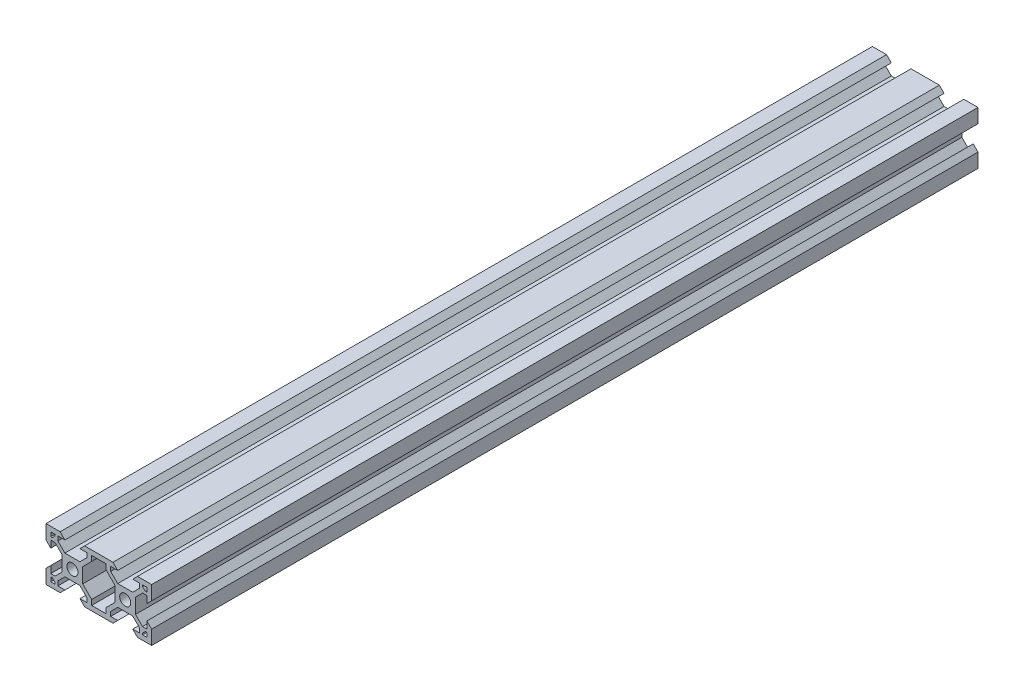
SolidWorks part; units mm, degrees
ref_plane "Front Plane" through (0, 0, 0) normal (0, 0, 1) x (1, 0, 0)
ref_plane "Top Plane" through (0, 0, 0) normal (0, 1, 0) x (1, 0, 0)
ref_plane "Right Plane" through (0, 0, 0) normal (1, 0, 0) x (0, 0, -1)
sketch "Sketch1" plane through (0, 0, 0) normal (0, 0, 1) x (1, 0, 0)
  line L0 (0, 0) -> (0, 5.36)
  line L1 (0, 20) -> (5.36, 20)
  line L3 (20, 0) -> (14.64, 0)
  line L4 (0, 10) -> (20, 10) construction
  line L5 (5.36, 0) -> (0, 0)
  line L6 (4.5007, 18.2) -> (7.16, 18.2)
  line L7 (17.3007, 3.76) -> (17.3007, 1.8)
  line L8 (15.4993, 1.8) -> (12.84, 1.8)
  line L9 (20, 0) -> (0, 0) construction
  line L10 (7.16, 1.8) -> (4.5007, 1.8)
  line L11 (15.4993, 3.44) -> (12.84, 6.0993)
  line L12 (4.5007, 16.56) -> (7.16, 13.9007)
  line L13 (13.9007, 12.84) -> (13.9007, 7.16)
  line L14 (12.84, 13.9007) -> (7.16, 13.9007)
  line L15 (6.0993, 12.84) -> (6.0993, 7.16)
  line L16 (7.16, 6.0993) -> (12.84, 6.0993)
  line L17 (4.5007, 16.56) -> (4.5007, 18.2)
  line L18 (3.44, 15.4993) -> (1.8, 15.4993)
  line L19 (4.5007, 3.44) -> (4.5007, 1.8)
  line L20 (3.44, 4.5007) -> (1.8, 4.5007)
  line L21 (15.4993, 3.44) -> (15.4993, 1.8)
  line L23 (17.3007, 1.8) -> (22.7007, 1.8)
  line L24 (15.4993, 16.56) -> (15.4993, 18.2)
  line L25 (7.16, 18.2) -> (5.36, 20)
  line L26 (12.84, 1.8) -> (14.64, 0)
  line L27 (7.16, 1.8) -> (5.36, 0)
  line L28 (12.84, 18.2) -> (14.64, 20)
  line L29 (1.8, 7.16) -> (0, 5.36)
  line L30 (1.8, 12.84) -> (0, 14.64)
  line L31 (22.7007, 1.8) -> (22.7007, 3.76)
  line L32 (17.3007, 16.24) -> (17.3007, 18.2)
  line L33 (17.3007, 18.2) -> (22.6993, 18.2)
  line L34 (22.6993, 18.2) -> (22.6993, 16.24)
  line L35 (38.2013, 12.8423) -> (40.001, 14.6427)
  line L36 (38.2024, 7.1623) -> (40.0028, 5.3627)
  line L37 (27.16, 18.2) -> (25.36, 20)
  line L38 (32.84, 1.8) -> (34.64, 0)
  line L39 (27.16, 1.8) -> (25.36, 0)
  line L40 (32.84, 18.2) -> (34.64, 20)
  line L41 (24.5013, 16.5597) -> (24.5009, 18.2)
  line L42 (1.8, 18.2) -> (3.4307, 18.2)
  line L43 (3.4307, 18.2) -> (3.4307, 17.63)
  line L44 (24.5038, 3.4397) -> (24.5041, 1.8)
  line L45 (36.5629, 4.5027) -> (38.2029, 4.503)
  line L46 (35.5025, 3.4418) -> (35.5028, 1.8)
  line L47 (36.5608, 15.5014) -> (38.2008, 15.5017)
  line L48 (35.4999, 16.5618) -> (35.4996, 18.2)
  line L49 (32.8426, 6.1006) -> (27.1626, 6.0995)
  line L50 (33.902, 12.8415) -> (33.9031, 7.1615)
  line L51 (27.1611, 13.9009) -> (32.8411, 13.902)
  line L52 (26.1007, 12.84) -> (26.1007, 7.16)
  line L53 (1.8, 4.5007) -> (1.8, 7.16)
  line L54 (24.5038, 3.4397) -> (27.1626, 6.0995)
  line L55 (35.5025, 3.4418) -> (32.8426, 6.1006)
  line L56 (36.5629, 4.5027) -> (33.9031, 7.1615)
  line L57 (24.5041, 1.8) -> (27.16, 1.8)
  line L58 (3.4307, 17.63) -> (2.37, 16.5693)
  line L59 (3.44, 4.5007) -> (6.0993, 7.16)
  line L60 (35.4996, 18.2) -> (32.84, 18.2)
  line L61 (20, 0) -> (25.36, 0)
  line L62 (39.9999, 20) -> (34.64, 20)
  line L63 (40.0038, 0) -> (40.0028, 5.3627)
  line L64 (1.8, 12.84) -> (1.8, 15.4993)
  line L65 (1.8, 1.8) -> (1.8, 18.2) construction
  line L66 (0, 14.64) -> (0, 20)
  line L67 (0, 0) -> (0, 20) construction
  line L68 (14.64, 20) -> (20, 20)
  line L69 (0, 20) -> (20, 20) construction
  line L70 (12.84, 18.2) -> (15.4993, 18.2)
  line L71 (1.8, 18.2) -> (18.2, 18.2) construction
  line L72 (25.36, 20) -> (20, 20)
  line L73 (27.16, 18.2) -> (24.5009, 18.2)
  line L74 (38.2013, 12.8423) -> (38.2008, 15.5017)
  line L75 (40.001, 14.6427) -> (39.9999, 20)
  line L76 (32.84, 1.8) -> (35.5028, 1.8)
  line L77 (34.64, 0) -> (40.0038, 0)
  line L78 (38.2029, 4.503) -> (38.2024, 7.1623)
  line L79 (35.4999, 16.5618) -> (32.8411, 13.902)
  line L80 (4.5007, 3.44) -> (7.16, 6.0993)
  line L81 (2.37, 16.5693) -> (1.8, 16.5693)
  line L82 (18.2, 1.8) -> (1.8, 1.8) construction
  line L83 (18.2, 18.2) -> (18.2, 1.8) construction
  line L84 (1.8, 16.5693) -> (1.8, 18.2)
  line L85 (20, 20) -> (20, 0) construction
  line L86 (1.8, 3.4307) -> (1.8, 1.8)
  line L87 (2.37, 3.4307) -> (1.8, 3.4307)
  line L88 (3.4307, 2.37) -> (2.37, 3.4307)
  line L89 (3.4307, 1.8) -> (3.4307, 2.37)
  line L90 (1.8, 1.8) -> (3.4307, 1.8)
  line L91 (13.9007, 7.16) -> (17.3007, 3.76)
  line L92 (20, 20) -> (20, -0.3542) construction
  line L93 (38.2, 1.8) -> (36.5693, 1.8)
  line L94 (36.5693, 1.8) -> (36.5693, 2.37)
  line L95 (36.5693, 2.37) -> (37.63, 3.4307)
  line L96 (37.63, 3.4307) -> (38.2, 3.4307)
  line L97 (38.2, 3.4307) -> (38.2, 1.8)
  line L98 (38.2, 16.5693) -> (38.2, 18.2)
  line L99 (37.63, 16.5693) -> (38.2, 16.5693)
  line L100 (36.5693, 17.63) -> (37.63, 16.5693)
  line L101 (36.5693, 18.2) -> (36.5693, 17.63)
  line L102 (38.2, 18.2) -> (36.5693, 18.2)
  line L103 (6.0993, 12.84) -> (3.44, 15.4993)
  line L104 (13.9007, 12.84) -> (17.3007, 16.24)
  line L105 (12.84, 13.9007) -> (15.4993, 16.56)
  line L106 (33.902, 12.8415) -> (36.5608, 15.5014)
  line L108 (27.1611, 13.9009) -> (24.5013, 16.5597)
  line L109 (26.1007, 12.84) -> (22.6993, 16.24)
  line L110 (26.1007, 7.16) -> (22.7007, 3.76)
  circle A0 centre (10, 10) radius 2.1
  circle A1 centre (30, 10) radius 2.1
  point P14 (17.3007, 3.76)
  point P81 (0, 0)
  point P82 (0, 0)
  point P112 (17.3007, 1.8)
  dimension "D3" = 4.2
  dimension "D1" = 20
  dimension "D2" = 20
  dimension "D5" = 5.4
  dimension "D7" = 1.07
  dimension "D8" = 45
  dimension "D9" = 1.5
  dimension "D10" = 4.5007
  dimension "D11" = 5.68
  dimension "D12" = 5.68
  dimension "D13" = 5.68
  dimension "D14" = 5.68
  dimension "D15" = 1.64
  dimension "D16" = 1.64
  dimension "D17" = 1.64
  dimension "D18" = 1.64
  dimension "D19" = 1.64
  dimension "D20" = 15.4993
  dimension "D21" = 1.07
  dimension "D22" = 1.64
  dimension "D23" = 45
  dimension "D24" = 45
  dimension "D25" = 1.5
  dimension "D26" = 45
  dimension "D27" = 45
  dimension "D28" = 45
  dimension "D4" = 1.8
extrude "Boss-Extrude1" add sketch "Sketch1" against normal blind 313
